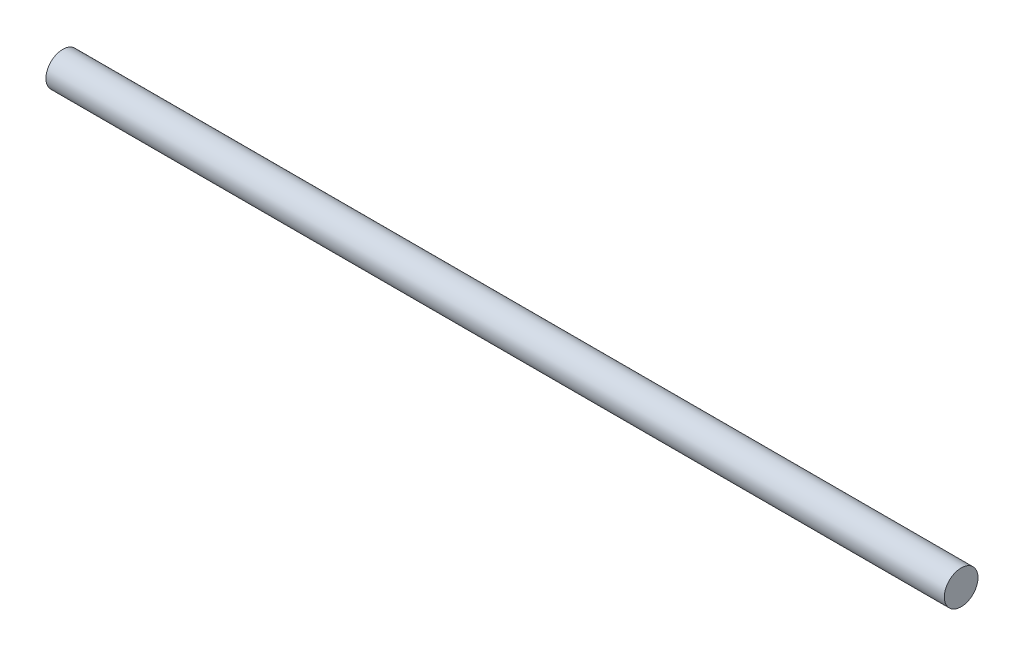
SolidWorks part; units mm, degrees
ref_plane "Front Plane" through (0, 0, 0) normal (0, 0, 1) x (1, 0, 0)
ref_plane "Top Plane" through (0, 0, 0) normal (0, 1, 0) x (1, 0, 0)
ref_plane "Right Plane" through (0, 0, 0) normal (1, 0, 0) x (0, 0, -1)
sketch "Sketch1" plane through (0, 0, 0) normal (1, 0, 0) x (0, 0, -1)
  circle A1 centre (0, 0) radius 1.5
extrude "Boss-Extrude1" add sketch "Sketch1" along normal blind 80
